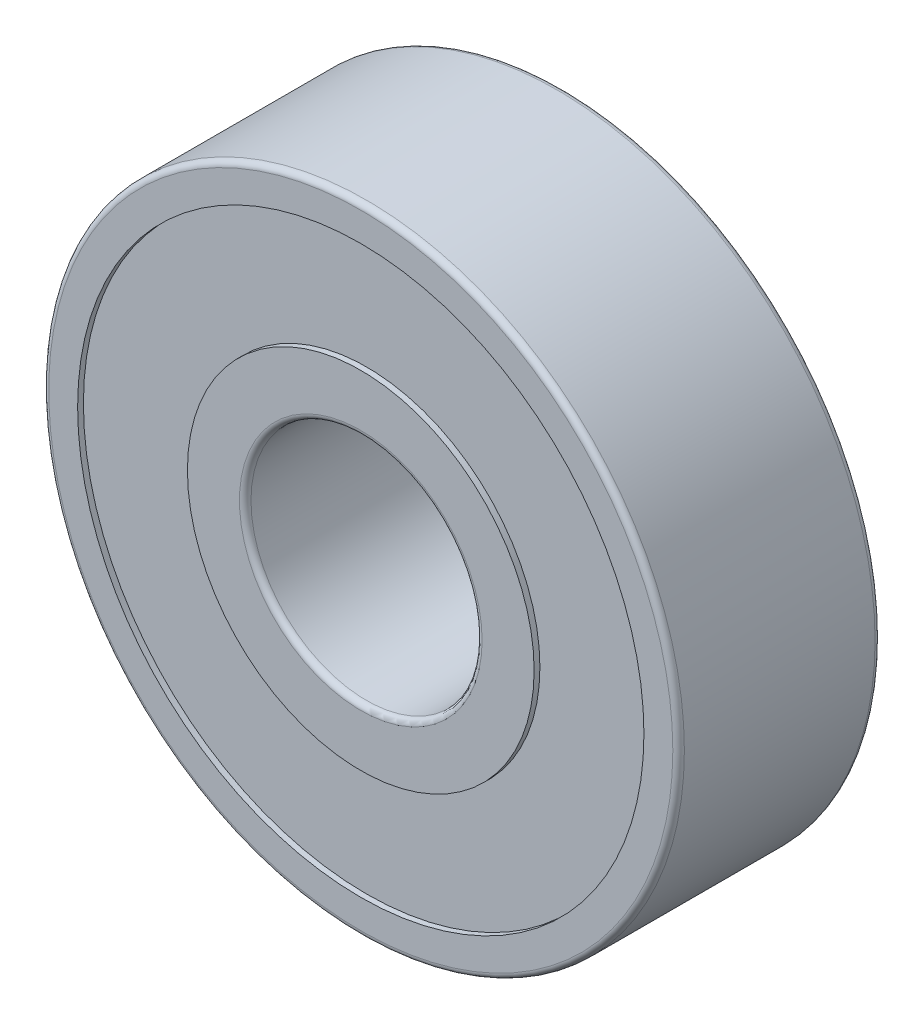
SolidWorks part; units mm, degrees
ref_plane "Front Plane" through (0, 0, 0) normal (0, 0, 1) x (1, 0, 0)
ref_plane "Top Plane" through (0, 0, 0) normal (0, 1, 0) x (1, 0, 0)
ref_plane "Right Plane" through (0, 0, 0) normal (1, 0, 0) x (0, 0, -1)
sketch "Sketch1" plane through (0, 0, 0) normal (0, 0, 1) x (1, 0, 0)
  circle A0 centre (0, 0) radius 11
  circle A1 centre (0, 0) radius 4
  dimension "D1" = 22
  dimension "D2" = 8
extrude "Boss-Extrude1" add sketch "Sketch1" along normal blind 7
sketch "Sketch2" plane through (0, 0, 7) normal (0, 0, 1) x (1, 0, 0)
  circle A0 centre (0, 0) radius 6
  circle A1 centre (0, 0) radius 9.8
  circle A2 centre (0, 0) radius 11 construction
  circle A3 centre (0, 0) radius 4 construction
  dimension "D1" = 1.2
  dimension "D2" = 2
extrude "Cut-Extrude1" cut sketch "Sketch2" against normal blind 0.2
ref_plane "Plane1" through (0, 0, 3.5) normal (0, 0, 1) x (1, 0, 0)
mirror "Mirror1" about plane through (0, 0, 3.5) normal (0, 0, 1) of "Cut-Extrude1"
fillet "Fillet1" radius 0.2 4 edges at (4, 0, 0) (4, 0, 7) (11, 0, 0) (11, 0, 7)
